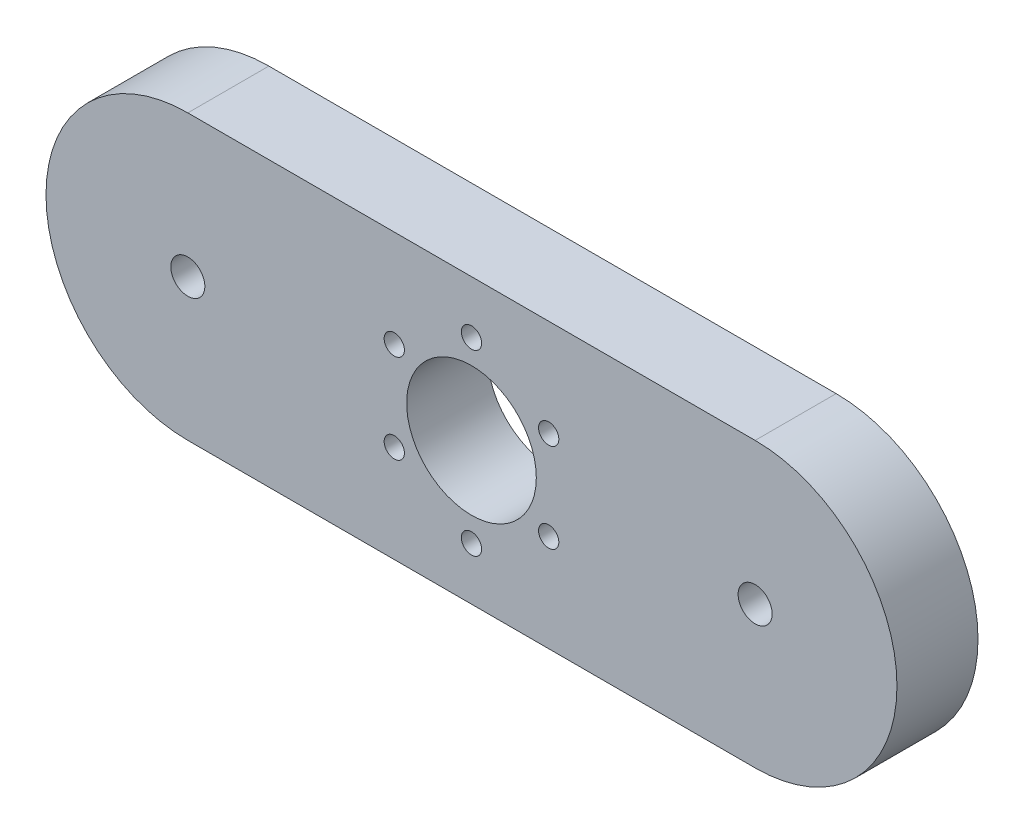
SolidWorks part; units mm, degrees
ref_plane "Ön Düzlem" through (0, 0, 0) normal (0, 0, 1) x (1, 0, 0)
ref_plane "Üst Düzlem" through (0, 0, 0) normal (0, 1, 0) x (1, 0, 0)
ref_plane "Sağ Düzlem" through (0, 0, 0) normal (1, 0, 0) x (0, 0, -1)
sketch "Çizim1" plane through (0, 0, 0) normal (0, 0, 1) x (1, 0, 0)
  line L0 (-35, 0) -> (35, 0) construction
  line L1 (-35, 17.5) -> (35, 17.5)
  line L2 (-35, -17.5) -> (35, -17.5)
  arc A0 (-35, 17.5) -> (-35, -17.5) centre (-35, 0) ccw
  arc A1 (35, -17.5) -> (35, 17.5) centre (35, 0) ccw
  circle A2 centre (0, 0) radius 8
  circle A3 centre (-35, 0) radius 2.1
  circle A4 centre (0, 11) radius 1.25
  circle A5 centre (9.5263, 5.5) radius 1.25
  circle A6 centre (9.5263, -5.5) radius 1.25
  circle A7 centre (0, -11) radius 1.25
  circle A8 centre (-9.5263, -5.5) radius 1.25
  circle A9 centre (-9.5263, 5.5) radius 1.25
  circle A10 centre (35, 0) radius 2.1
  point P2 (0, 0)
  point P26 (0, 0)
  point P30 (0, 0)
  dimension "D1" = 11
  dimension "D2" = 70
  dimension "D3" = 6
extrude "Yükseklik-Ekstrüzyon1" add sketch "Çizim1" along normal blind 10
